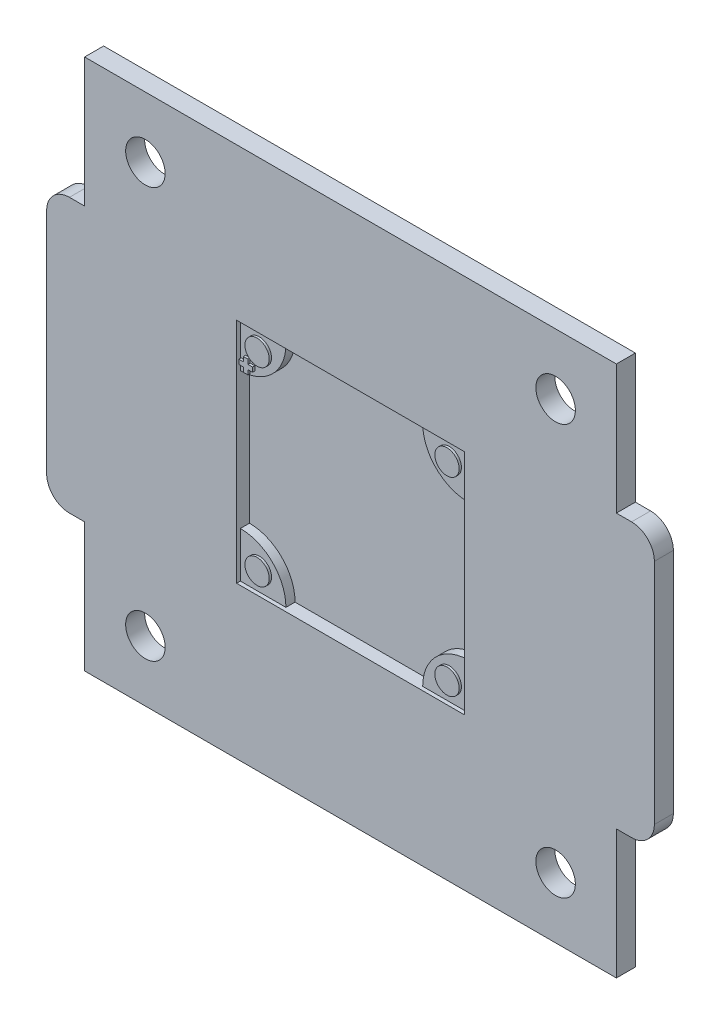
SolidWorks part; units mm, degrees
ref_plane "前视基准面" through (0, 0, 0) normal (0, 0, 1) x (1, 0, 0)
ref_plane "上视基准面" through (0, 0, 0) normal (0, 1, 0) x (1, 0, 0)
ref_plane "右视基准面" through (0, 0, 0) normal (1, 0, 0) x (0, 0, -1)
sketch "草图1" plane through (0, 0, 0) normal (0, 0, 1) x (1, 0, 0)
  line L0 (35, 70) -> (35, 0) construction
  line L1 (0, 0) -> (70, 0)
  line L2 (0, 0) -> (0, 70)
  line L3 (0, 70) -> (70, 70)
  line L4 (70, 0) -> (70, 70)
  line L5 (0, 35) -> (70, 35) construction
  line L6 (70, 17) -> (72, 17)
  line L7 (0, 53) -> (-2, 53)
  line L8 (0, 53) -> (0, 17)
  line L9 (0, 17) -> (-2, 17)
  line L10 (-5, 50) -> (-5, 20)
  line L11 (75, 50) -> (75, 20)
  line L12 (70, 53) -> (72, 53)
  line L13 (70, 53) -> (70, 17)
  arc A0 (-2, 17) -> (-5, 20) centre (-2, 20) cw
  arc A1 (-2, 53) -> (-5, 50) centre (-2, 50) ccw
  arc A2 (72, 17) -> (75, 20) centre (72, 20) ccw
  arc A3 (72, 53) -> (75, 50) centre (72, 50) cw
  point P6 (35, 70)
  point P10 (0, 35)
  point P15 (-5, 35)
  point P18 (-5, 17)
  point P21 (-5, 53)
  dimension "D4" = 3
  dimension "D1" = 70
  dimension "D2" = 5
  dimension "D3" = 36
extrude "凸台-拉伸1" add sketch "草图1" along normal blind 2.5 contours L7 A1 L10 A0 L9 L2 | L1 L4 L3 L2 | A3 L12 L4 L6 A2 L11
sketch "草图2" plane through (0, 0, 2.5) normal (0, 0, 1) x (1, 0, 0)
  line L0 (0, 70) -> (70, 70) construction
  line L1 (35, 70) -> (35, 0) construction
  line L2 (0, 0) -> (70, 0) construction
  line L3 (-5, 50) -> (-5, 20) construction
  line L4 (-5, 35) -> (75, 35) construction
  line L5 (75, 50) -> (75, 20) construction
  line L7 (20, 50) -> (50, 50)
  line L8 (20, 50) -> (20, 20)
  line L9 (20, 20) -> (50, 20)
  line L10 (50, 50) -> (50, 20)
  point P6 (35, 70)
  point P17 (35, 50)
  point P18 (20, 35)
  dimension "D1" = 30
extrude "切除-拉伸1" cut sketch "草图2" against normal blind 1.7
sketch "草图3" plane through (0, 0, 2.5) normal (0, 0, 1) x (1, 0, 0)
  line L0 (0, 70) -> (0, 0) construction
  line L1 (0, 70) -> (70, 70) construction
  line L2 (0, 53) -> (0, 70) construction
  line L3 (70, 0) -> (70, 70) construction
  line L4 (70, 53) -> (70, 70) construction
  line L5 (0, 35) -> (70, 35) construction
  line L6 (35, 70) -> (35, 0) construction
  line L7 (0, 0) -> (70, 0) construction
  circle A0 centre (8, 62) radius 2.6
  circle A1 centre (62, 62) radius 2.6
  circle A2 centre (8, 8) radius 2.6
  circle A3 centre (62, 8) radius 2.6
  point P18 (35, 70)
  point P19 (0, 35)
  dimension "D3" = 5.2
  dimension "D1" = 8
  dimension "D2" = 8
extrude "切除-拉伸2" cut sketch "草图3" against normal blind 3
sketch "草图4" plane through (0, 0, 0) normal (0, 0, 1) x (1, 0, 0)
  line L0 (20, 35) -> (50, 35) construction
  line L1 (20, 50) -> (50, 50) construction
  line L2 (20, 50) -> (20, 20) construction
  line L3 (20, 20) -> (50, 20) construction
  line L4 (50, 50) -> (50, 20) construction
  line L5 (35, 50) -> (35, 20) construction
  line L6 (20, 44) -> (20, 50)
  line L7 (20, 50) -> (26, 50)
  line L8 (50, 44) -> (50, 50)
  line L9 (50, 50) -> (44, 50)
  line L10 (50, 20) -> (44, 20)
  line L11 (50, 26) -> (50, 20)
  line L12 (20, 26) -> (20, 20)
  line L13 (20, 20) -> (26, 20)
  arc A0 (26, 50) -> (20, 44) centre (20, 50) cw
  arc A1 (44, 50) -> (50, 44) centre (50, 50) ccw
  arc A2 (44, 20) -> (50, 26) centre (50, 20) cw
  arc A3 (26, 20) -> (20, 26) centre (20, 20) ccw
  point P10 (35, 20)
  point P11 (20, 35)
  dimension "D1" = 6
extrude "凸台-拉伸2" add sketch "草图4" along normal blind 2
sketch "草图6" plane through (0, 0, 2) normal (0, 0, 1) x (1, 0, 0)
  line L0 (20, 35) -> (50, 35) construction
  line L1 (20, 50) -> (50, 50) construction
  line L2 (20, 50) -> (20, 20) construction
  line L3 (20, 20) -> (50, 20) construction
  line L4 (50, 50) -> (50, 20) construction
  line L5 (35, 50) -> (35, 20) construction
  line L6 (20.1, 45.5) -> (20.7, 45.5)
  line L7 (20.7, 45.5) -> (20.7, 46.1)
  line L8 (20.7, 46.1) -> (21.3, 46.1)
  line L9 (21.3, 46.1) -> (21.3, 45.5)
  line L10 (21.3, 45.5) -> (21.9, 45.5)
  line L11 (21.9, 45.5) -> (21.9, 44.9)
  line L12 (21.9, 44.9) -> (21.3, 44.9)
  line L13 (21.3, 44.9) -> (21.3, 44.3)
  line L14 (21.3, 44.3) -> (20.7, 44.3)
  line L15 (20.7, 44.3) -> (20.7, 44.9)
  line L16 (20.7, 44.9) -> (20.1, 44.9)
  line L17 (20.1, 44.9) -> (20.1, 45.5)
  circle A4 centre (22.5, 47.5) radius 1.6
  circle A5 centre (47.5, 47.5) radius 1.6
  circle A6 centre (47.5, 22.5) radius 1.6
  circle A7 centre (22.5, 22.5) radius 1.6
  point P10 (35, 20)
  point P11 (20, 35)
  point P31 (21, 46.1)
  dimension "D1" = 2.5
  dimension "D2" = 2.5
  dimension "D3" = 3.2
  dimension "D4" = 0.6
  dimension "D5" = 0.6
  dimension "D6" = 0.1
  dimension "D7" = 3.9
extrude "凸台-拉伸3" add sketch "草图6" along normal blind 0.3
